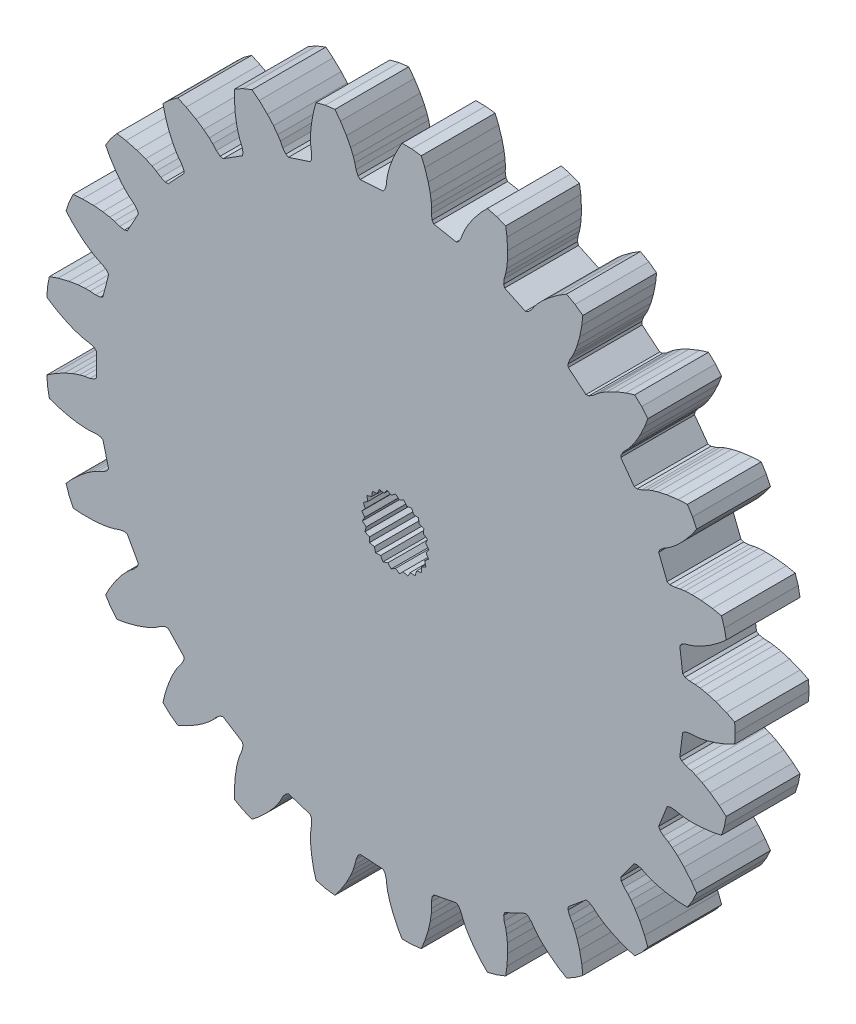
SolidWorks part; units mm, degrees
ref_plane "Front Plane" through (0, 0, 0) normal (0, 0, 1) x (1, 0, 0)
ref_plane "Top Plane" through (0, 0, 0) normal (0, 1, 0) x (1, 0, 0)
ref_plane "Right Plane" through (0, 0, 0) normal (1, 0, 0) x (0, 0, -1)
sketch "Model" plane through (0, 0, 0) normal (0, 0, 1) x (1, 0, 0)
  line L0 (28.0476, -8.5314) -> (28.3042, -7.7419)
  line L1 (28.3042, -7.7419) -> (28.4597, -6.9264)
  line L2 (28.4597, -6.9264) -> (27.8578, -6.4126)
  line L3 (27.8578, -6.4126) -> (27.0681, -5.8455)
  line L4 (27.0681, -5.8455) -> (26.3904, -5.4402)
  line L5 (26.3904, -5.4402) -> (25.8454, -5.1734)
  line L6 (25.8454, -5.1734) -> (25.4502, -5.0195)
  line L7 (25.4502, -5.0195) -> (24.9993, -4.8861)
  line L8 (24.9993, -4.8861) -> (24.6274, -4.699)
  line L9 (24.6274, -4.699) -> (24.4647, -4.4976)
  line L10 (24.4647, -4.4976) -> (24.7116, -2.5433)
  line L11 (24.7116, -2.5433) -> (24.9192, -2.3886)
  line L12 (24.9192, -2.3886) -> (25.326, -2.2999)
  line L13 (25.326, -2.2999) -> (25.7959, -2.2828)
  line L14 (25.7959, -2.2828) -> (26.217, -2.232)
  line L15 (26.217, -2.232) -> (26.8112, -2.1091)
  line L16 (26.8112, -2.1091) -> (27.5684, -1.8851)
  line L17 (27.5684, -1.8851) -> (28.4744, -1.5322)
  line L18 (28.4744, -1.5322) -> (29.1851, -1.1843)
  line L19 (29.1851, -1.1843) -> (29.2372, -0.3558)
  line L20 (29.2372, -0.3558) -> (29.1851, 0.4728)
  line L21 (29.1851, 0.4728) -> (28.4744, 0.8207)
  line L22 (28.4744, 0.8207) -> (27.5684, 1.1736)
  line L23 (27.5684, 1.1736) -> (26.8112, 1.3976)
  line L24 (26.8112, 1.3976) -> (26.217, 1.5205)
  line L25 (26.217, 1.5205) -> (25.7959, 1.5713)
  line L26 (25.7959, 1.5713) -> (25.326, 1.5884)
  line L27 (25.326, 1.5884) -> (24.9192, 1.6771)
  line L28 (24.9192, 1.6771) -> (24.7116, 1.8317)
  line L29 (24.7116, 1.8317) -> (24.4647, 3.7861)
  line L30 (24.4647, 3.7861) -> (24.6274, 3.9875)
  line L31 (24.6274, 3.9875) -> (24.9993, 4.1746)
  line L32 (24.9993, 4.1746) -> (25.4502, 4.308)
  line L33 (25.4502, 4.308) -> (25.8454, 4.4619)
  line L34 (25.8454, 4.4619) -> (26.3904, 4.7287)
  line L35 (26.3904, 4.7287) -> (27.0681, 5.134)
  line L36 (27.0681, 5.134) -> (27.8578, 5.7011)
  line L37 (27.8578, 5.7011) -> (28.4597, 6.2148)
  line L38 (28.4597, 6.2148) -> (28.3042, 7.0303)
  line L39 (28.3042, 7.0303) -> (28.0476, 7.8199)
  line L40 (28.0476, 7.8199) -> (27.2727, 7.9801)
  line L41 (27.2727, 7.9801) -> (26.3074, 8.0966)
  line L42 (26.3074, 8.0966) -> (25.5183, 8.1253)
  line L43 (25.5183, 8.1253) -> (24.9122, 8.0965)
  line L44 (24.9122, 8.0965) -> (24.4917, 8.041)
  line L45 (24.4917, 8.041) -> (24.0323, 7.9407)
  line L46 (24.0323, 7.9407) -> (23.6163, 7.9255)
  line L47 (23.6163, 7.9255) -> (23.3767, 8.0236)
  line L48 (23.3767, 8.0236) -> (22.6515, 9.8551)
  line L49 (22.6515, 9.8551) -> (22.759, 10.0907)
  line L50 (22.759, 10.0907) -> (23.0727, 10.3644)
  line L51 (23.0727, 10.3644) -> (23.4763, 10.6057)
  line L52 (23.4763, 10.6057) -> (23.8208, 10.8531)
  line L53 (23.8208, 10.8531) -> (24.2823, 11.2471)
  line L54 (24.2823, 11.2471) -> (24.8379, 11.8081)
  line L55 (24.8379, 11.8081) -> (25.4618, 12.5538)
  line L56 (25.4618, 12.5538) -> (25.917, 13.2011)
  line L57 (25.917, 13.2011) -> (25.5636, 13.9523)
  line L58 (25.5636, 13.9523) -> (25.1187, 14.6533)
  line L59 (25.1187, 14.6533) -> (24.3283, 14.6157)
  line L60 (24.3283, 14.6157) -> (23.3643, 14.4885)
  line L61 (23.3643, 14.4885) -> (22.5929, 14.3201)
  line L62 (22.5929, 14.3201) -> (22.013, 14.1415)
  line L63 (22.013, 14.1415) -> (21.6195, 13.9831)
  line L64 (21.6195, 13.9831) -> (21.1995, 13.7717)
  line L65 (21.1995, 13.7717) -> (20.8003, 13.6535)
  line L66 (20.8003, 13.6535) -> (20.5439, 13.689)
  line L67 (20.5439, 13.689) -> (19.386, 15.2826)
  line L68 (19.386, 15.2826) -> (19.4315, 15.5375)
  line L69 (19.4315, 15.5375) -> (19.6673, 15.8806)
  line L70 (19.6673, 15.8806) -> (19.9982, 16.2148)
  line L71 (19.9982, 16.2148) -> (20.2703, 16.54)
  line L72 (20.2703, 16.54) -> (20.6194, 17.0364)
  line L73 (20.6194, 17.0364) -> (21.018, 17.718)
  line L74 (21.018, 17.718) -> (21.4368, 18.5954)
  line L75 (21.4368, 18.5954) -> (21.7168, 19.3356)
  line L76 (21.7168, 19.3356) -> (21.1876, 19.9753)
  line L77 (21.1876, 19.9753) -> (20.5824, 20.5436)
  line L78 (20.5824, 20.5436) -> (19.8261, 20.3107)
  line L79 (19.8261, 20.3107) -> (18.9241, 19.9477)
  line L80 (18.9241, 19.9477) -> (18.2189, 19.5927)
  line L81 (18.2189, 19.5927) -> (17.7016, 19.2755)
  line L82 (17.7016, 19.2755) -> (17.3598, 19.0243)
  line L83 (17.3598, 19.0243) -> (17.0056, 18.7151)
  line L84 (17.0056, 18.7151) -> (16.6483, 18.5013)
  line L85 (16.6483, 18.5013) -> (16.3911, 18.4719)
  line L86 (16.3911, 18.4719) -> (14.8733, 19.7275)
  line L87 (14.8733, 19.7275) -> (14.854, 19.9857)
  line L88 (14.854, 19.9857) -> (14.997, 20.3767)
  line L89 (14.997, 20.3767) -> (15.2344, 20.7826)
  line L90 (15.2344, 20.7826) -> (15.4171, 21.1653)
  line L91 (15.4171, 21.1653) -> (15.6318, 21.7329)
  line L92 (15.6318, 21.7329) -> (15.8484, 22.4922)
  line L93 (15.8484, 22.4922) -> (16.0359, 23.4463)
  line L94 (16.0359, 23.4463) -> (16.1229, 24.2328)
  line L95 (16.1229, 24.2328) -> (15.4513, 24.7208)
  line L96 (15.4513, 24.7208) -> (14.7238, 25.1207)
  line L97 (14.7238, 25.1207) -> (14.0492, 24.707)
  line L98 (14.0492, 24.707) -> (13.2658, 24.1312)
  line L99 (13.2658, 24.1312) -> (12.671, 23.6119)
  line L100 (12.671, 23.6119) -> (12.2488, 23.176)
  line L101 (12.2488, 23.176) -> (11.9803, 22.8477)
  line L102 (11.9803, 22.8477) -> (11.7141, 22.4601)
  line L103 (11.7141, 22.4601) -> (11.4212, 22.1642)
  line L104 (11.4212, 22.1642) -> (11.1794, 22.0718)
  line L105 (11.1794, 22.0718) -> (9.397, 22.9105)
  line L106 (9.397, 22.9105) -> (9.3141, 23.1558)
  line L107 (9.3141, 23.1558) -> (9.3554, 23.57)
  line L108 (9.3554, 23.57) -> (9.4844, 24.0222)
  line L109 (9.4844, 24.0222) -> (9.5662, 24.4384)
  line L110 (9.5662, 24.4384) -> (9.6329, 25.0415)
  line L111 (9.6329, 25.0415) -> (9.6539, 25.8308)
  line L112 (9.6539, 25.8308) -> (9.5982, 26.8015)
  line L113 (9.5982, 26.8015) -> (9.4869, 27.585)
  line L114 (9.4869, 27.585) -> (8.7151, 27.8906)
  line L115 (8.7151, 27.8906) -> (7.9109, 28.0971)
  line L116 (7.9109, 28.0971) -> (7.3604, 27.5286)
  line L117 (7.3604, 27.5286) -> (6.7448, 26.776)
  line L118 (6.7448, 26.776) -> (6.2978, 26.1252)
  line L119 (6.2978, 26.1252) -> (5.9973, 25.598)
  line L120 (5.9973, 25.598) -> (5.8189, 25.2132)
  line L121 (5.8189, 25.2132) -> (5.6574, 24.7716)
  line L122 (5.6574, 24.7716) -> (5.4473, 24.4121)
  line L123 (5.4473, 24.4121) -> (5.2361, 24.2624)
  line L124 (5.2361, 24.2624) -> (3.3011, 24.6315)
  line L125 (3.3011, 24.6315) -> (3.1599, 24.8485)
  line L126 (3.1599, 24.8485) -> (3.0968, 25.26)
  line L127 (3.0968, 25.26) -> (3.1093, 25.7301)
  line L128 (3.1093, 25.7301) -> (3.085, 26.1535)
  line L129 (3.085, 26.1535) -> (2.9997, 26.7543)
  line L130 (2.9997, 26.7543) -> (2.8237, 27.524)
  line L131 (2.8237, 27.524) -> (2.5284, 28.4504)
  line L132 (2.5284, 28.4504) -> (2.2258, 29.1816)
  line L133 (2.2258, 29.1816) -> (1.4021, 29.2856)
  line L134 (1.4021, 29.2856) -> (0.5719, 29.2856)
  line L135 (0.5719, 29.2856) -> (0.1801, 28.5981)
  line L136 (0.1801, 28.5981) -> (-0.229, 27.7161)
  line L137 (-0.229, 27.7161) -> (-0.5001, 26.9745)
  line L138 (-0.5001, 26.9745) -> (-0.6601, 26.3891)
  line L139 (-0.6601, 26.3891) -> (-0.7372, 25.9721)
  line L140 (-0.7372, 25.9721) -> (-0.7838, 25.5042)
  line L141 (-0.7838, 25.5042) -> (-0.8979, 25.1038)
  line L142 (-0.8979, 25.1038) -> (-1.0652, 24.9063)
  line L143 (-1.0652, 24.9063) -> (-3.0312, 24.7826)
  line L144 (-3.0312, 24.7826) -> (-3.222, 24.9576)
  line L145 (-3.222, 24.9576) -> (-3.3854, 25.3405)
  line L146 (-3.3854, 25.3405) -> (-3.4902, 25.7989)
  line L147 (-3.4902, 25.7989) -> (-3.619, 26.203)
  line L148 (-3.619, 26.203) -> (-3.8511, 26.7637)
  line L149 (-3.8511, 26.7637) -> (-4.213, 27.4654)
  line L150 (-4.213, 27.4654) -> (-4.7294, 28.2892)
  line L151 (-4.7294, 28.2892) -> (-5.2043, 28.9222)
  line L152 (-5.2043, 28.9222) -> (-6.028, 28.8182)
  line L153 (-6.028, 28.8182) -> (-6.8321, 28.6117)
  line L154 (-6.8321, 28.6117) -> (-7.0407, 27.8483)
  line L155 (-7.0407, 27.8483) -> (-7.2175, 26.8923)
  line L156 (-7.2175, 26.8923) -> (-7.2957, 26.1066)
  line L157 (-7.2957, 26.1066) -> (-7.305, 25.4998)
  line L158 (-7.305, 25.4998) -> (-7.2761, 25.0767)
  line L159 (-7.2761, 25.0767) -> (-7.2048, 24.6119)
  line L160 (-7.2048, 24.6119) -> (-7.2157, 24.1957)
  line L161 (-7.2157, 24.1957) -> (-7.3287, 23.9628)
  line L162 (-7.3287, 23.9628) -> (-9.2022, 23.354)
  line L163 (-9.2022, 23.354) -> (-9.4305, 23.4761)
  line L164 (-9.4305, 23.4761) -> (-9.684, 23.8064)
  line L165 (-9.684, 23.8064) -> (-9.8995, 24.2243)
  line L166 (-9.8995, 24.2243) -> (-10.1248, 24.5836)
  line L167 (-10.1248, 24.5836) -> (-10.489, 25.069)
  line L168 (-10.489, 25.069) -> (-11.014, 25.6587)
  line L169 (-11.014, 25.6587) -> (-11.7191, 26.3282)
  line L170 (-11.7191, 26.3282) -> (-12.3365, 26.8232)
  line L171 (-12.3365, 26.8232) -> (-13.1084, 26.5176)
  line L172 (-13.1084, 26.5176) -> (-13.8359, 26.1176)
  line L173 (-13.8359, 26.1176) -> (-13.8481, 25.3264)
  line L174 (-13.8481, 25.3264) -> (-13.7816, 24.3564)
  line L175 (-13.7816, 24.3564) -> (-13.662, 23.5759)
  line L176 (-13.662, 23.5759) -> (-13.5201, 22.9859)
  line L177 (-13.5201, 22.9859) -> (-13.3868, 22.5833)
  line L178 (-13.3868, 22.5833) -> (-13.2022, 22.1508)
  line L179 (-13.2022, 22.1508) -> (-13.1093, 21.745)
  line L180 (-13.1093, 21.745) -> (-13.1608, 21.4913)
  line L181 (-13.1608, 21.4913) -> (-14.824, 20.4358)
  line L182 (-14.824, 20.4358) -> (-15.0755, 20.4972)
  line L183 (-15.0755, 20.4972) -> (-15.4031, 20.7541)
  line L184 (-15.4031, 20.7541) -> (-15.7158, 21.1052)
  line L185 (-15.7158, 21.1052) -> (-16.0234, 21.3973)
  line L186 (-16.0234, 21.3973) -> (-16.4969, 21.7769)
  line L187 (-16.4969, 21.7769) -> (-17.1521, 22.2174)
  line L188 (-17.1521, 22.2174) -> (-18.0015, 22.6906)
  line L189 (-18.0015, 22.6906) -> (-18.7226, 23.0165)
  line L190 (-18.7226, 23.0165) -> (-19.3942, 22.5285)
  line L191 (-19.3942, 22.5285) -> (-19.9994, 21.9602)
  line L192 (-19.9994, 21.9602) -> (-19.8144, 21.1907)
  line L193 (-19.8144, 21.1907) -> (-19.5089, 20.2677)
  line L194 (-19.5089, 20.2677) -> (-19.1989, 19.5416)
  line L195 (-19.1989, 19.5416) -> (-18.9147, 19.0054)
  line L196 (-18.9147, 19.0054) -> (-18.6855, 18.6485)
  line L197 (-18.6855, 18.6485) -> (-18.3991, 18.2756)
  line L198 (-18.3991, 18.2756) -> (-18.2082, 17.9056)
  line L199 (-18.2082, 17.9056) -> (-18.195, 17.647)
  line L200 (-18.195, 17.647) -> (-19.5434, 16.2111)
  line L201 (-19.5434, 16.2111) -> (-19.8023, 16.208)
  line L202 (-19.8023, 16.208) -> (-20.1836, 16.3753)
  line L203 (-20.1836, 16.3753) -> (-20.5738, 16.6377)
  line L204 (-20.5738, 16.6377) -> (-20.9443, 16.8441)
  line L205 (-20.9443, 16.8441) -> (-21.4973, 17.094)
  line L206 (-21.4973, 17.094) -> (-22.2415, 17.3578)
  line L207 (-22.2415, 17.3578) -> (-23.1819, 17.6048)
  line L208 (-23.1819, 17.6048) -> (-23.9614, 17.7411)
  line L209 (-23.9614, 17.7411) -> (-24.4906, 17.1015)
  line L210 (-24.4906, 17.1015) -> (-24.9354, 16.4005)
  line L211 (-24.9354, 16.4005) -> (-24.5649, 15.7013)
  line L212 (-24.5649, 15.7013) -> (-24.0393, 14.8832)
  line L213 (-24.0393, 14.8832) -> (-23.5585, 14.257)
  line L214 (-23.5585, 14.257) -> (-23.1499, 13.8083)
  line L215 (-23.1499, 13.8083) -> (-22.8392, 13.5197)
  line L216 (-22.8392, 13.5197) -> (-22.469, 13.2296)
  line L217 (-22.469, 13.2296) -> (-22.1921, 12.9188)
  line L218 (-22.1921, 12.9188) -> (-22.115, 12.6716)
  line L219 (-22.115, 12.6716) -> (-23.064, 10.9454)
  line L220 (-23.064, 10.9454) -> (-23.314, 10.8781)
  line L221 (-23.314, 10.8781) -> (-23.7248, 10.9453)
  line L222 (-23.7248, 10.9453) -> (-24.1681, 11.1024)
  line L223 (-24.1681, 11.1024) -> (-24.5782, 11.2102)
  line L224 (-24.5782, 11.2102) -> (-25.176, 11.3147)
  line L225 (-25.176, 11.3147) -> (-25.9624, 11.3851)
  line L226 (-25.9624, 11.3851) -> (-26.9347, 11.3905)
  line L227 (-26.9347, 11.3905) -> (-27.7236, 11.3287)
  line L228 (-27.7236, 11.3287) -> (-28.0771, 10.5775)
  line L229 (-28.0771, 10.5775) -> (-28.3337, 9.788)
  line L230 (-28.3337, 9.788) -> (-27.8009, 9.2028)
  line L231 (-27.8009, 9.2028) -> (-27.0884, 8.5412)
  line L232 (-27.0884, 8.5412) -> (-26.4669, 8.0542)
  line L233 (-26.4669, 8.0542) -> (-25.9596, 7.7212)
  line L234 (-25.9596, 7.7212) -> (-25.5868, 7.519)
  line L235 (-25.5868, 7.519) -> (-25.1562, 7.3301)
  line L236 (-25.1562, 7.3301) -> (-24.8107, 7.0979)
  line L237 (-24.8107, 7.0979) -> (-24.6745, 6.8776)
  line L238 (-24.6745, 6.8776) -> (-25.1644, 4.9697)
  line L239 (-25.1644, 4.9697) -> (-25.3898, 4.8423)
  line L240 (-25.3898, 4.8423) -> (-25.8045, 4.8052)
  line L241 (-25.8045, 4.8052) -> (-26.2728, 4.8472)
  line L242 (-26.2728, 4.8472) -> (-26.6969, 4.8495)
  line L243 (-26.6969, 4.8495) -> (-27.3019, 4.8021)
  line L244 (-27.3019, 4.8021) -> (-28.0812, 4.6748)
  line L245 (-28.0812, 4.6748) -> (-29.0242, 4.4382)
  line L246 (-29.0242, 4.4382) -> (-29.773, 4.1821)
  line L247 (-29.773, 4.1821) -> (-29.9286, 3.3666)
  line L248 (-29.9286, 3.3666) -> (-29.9807, 2.5381)
  line L249 (-29.9807, 2.5381) -> (-29.3191, 2.1038)
  line L250 (-29.3191, 2.1038) -> (-28.4645, 1.6402)
  line L251 (-28.4645, 1.6402) -> (-27.7414, 1.323)
  line L252 (-27.7414, 1.323) -> (-27.1673, 1.1266)
  line L253 (-27.1673, 1.1266) -> (-26.7559, 1.0235)
  line L254 (-26.7559, 1.0235) -> (-26.2918, 0.9476)
  line L255 (-26.2918, 0.9476) -> (-25.8994, 0.8086)
  line L256 (-25.8994, 0.8086) -> (-25.7128, 0.6292)
  line L257 (-25.7128, 0.6292) -> (-25.7128, -1.3407)
  line L258 (-25.7128, -1.3407) -> (-25.8994, -1.5201)
  line L259 (-25.8994, -1.5201) -> (-26.2918, -1.6591)
  line L260 (-26.2918, -1.6591) -> (-26.7559, -1.735)
  line L261 (-26.7559, -1.735) -> (-27.1673, -1.8382)
  line L262 (-27.1673, -1.8382) -> (-27.7414, -2.0346)
  line L263 (-27.7414, -2.0346) -> (-28.4645, -2.3517)
  line L264 (-28.4645, -2.3517) -> (-29.3191, -2.8154)
  line L265 (-29.3191, -2.8154) -> (-29.9807, -3.2496)
  line L266 (-29.9807, -3.2496) -> (-29.9286, -4.0782)
  line L267 (-29.9286, -4.0782) -> (-29.773, -4.8937)
  line L268 (-29.773, -4.8937) -> (-29.0242, -5.1497)
  line L269 (-29.0242, -5.1497) -> (-28.0812, -5.3863)
  line L270 (-28.0812, -5.3863) -> (-27.3019, -5.5137)
  line L271 (-27.3019, -5.5137) -> (-26.6969, -5.5611)
  line L272 (-26.6969, -5.5611) -> (-26.2728, -5.5587)
  line L273 (-26.2728, -5.5587) -> (-25.8045, -5.5168)
  line L274 (-25.8045, -5.5168) -> (-25.3898, -5.5538)
  line L275 (-25.3898, -5.5538) -> (-25.1644, -5.6812)
  line L276 (-25.1644, -5.6812) -> (-24.6745, -7.5892)
  line L277 (-24.6745, -7.5892) -> (-24.8107, -7.8094)
  line L278 (-24.8107, -7.8094) -> (-25.1562, -8.0416)
  line L279 (-25.1562, -8.0416) -> (-25.5868, -8.2305)
  line L280 (-25.5868, -8.2305) -> (-25.9596, -8.4327)
  line L281 (-25.9596, -8.4327) -> (-26.4669, -8.7657)
  line L282 (-26.4669, -8.7657) -> (-27.0884, -9.2527)
  line L283 (-27.0884, -9.2527) -> (-27.8009, -9.9144)
  line L284 (-27.8009, -9.9144) -> (-28.3337, -10.4995)
  line L285 (0.0008, 2.8698) -> (-0.3313, 2.6039)
  line L286 (0.0008, 2.8698) -> (0.3329, 2.6039)
  line L287 (0.7207, 2.7788) -> (0.3329, 2.6039)
  line L288 (0.7207, 2.7788) -> (0.9763, 2.4387)
  line L289 (1.3955, 2.5117) -> (0.9763, 2.4387)
  line L290 (1.3955, 2.5117) -> (1.5584, 2.1187)
  line L291 (1.9826, 2.0851) -> (1.5584, 2.1187)
  line L292 (1.9826, 2.0851) -> (2.0426, 1.6639)
  line L293 (2.4451, 1.526) -> (2.0426, 1.6639)
  line L294 (2.4451, 1.526) -> (2.3986, 1.1031)
  line L295 (2.7541, 0.8694) -> (2.3986, 1.1031)
  line L296 (2.7541, 0.8694) -> (2.6038, 0.4713)
  line L297 (2.8901, 0.1565) -> (2.6038, 0.4713)
  line L298 (2.8901, 0.1565) -> (2.6456, -0.1916)
  line L299 (2.8445, -0.5677) -> (2.6456, -0.1916)
  line L300 (2.8445, -0.5677) -> (2.5211, -0.8441)
  line L301 (2.6203, -1.2579) -> (2.5211, -0.8441)
  line L302 (2.6203, -1.2579) -> (2.2383, -1.4452)
  line L303 (2.2314, -1.8706) -> (2.2383, -1.4452)
  line L304 (2.2314, -1.8706) -> (1.8148, -1.957)
  line L305 (1.7024, -2.3673) -> (1.8148, -1.957)
  line L306 (1.7024, -2.3673) -> (1.2774, -2.3474)
  line L307 (1.0665, -2.7169) -> (1.2774, -2.3474)
  line L308 (1.0665, -2.7169) -> (0.6598, -2.592)
  line L309 (0.3636, -2.8974) -> (0.6598, -2.592)
  line L310 (0.3636, -2.8974) -> (0.0008, -2.6752)
  line L311 (-0.3621, -2.8974) -> (0.0008, -2.6752)
  line L312 (-0.3621, -2.8974) -> (-0.6582, -2.592)
  line L313 (-1.0649, -2.7169) -> (-0.6582, -2.592)
  line L314 (-1.0649, -2.7169) -> (-1.2759, -2.3474)
  line L315 (-1.7009, -2.3673) -> (-1.2759, -2.3474)
  line L316 (-1.7009, -2.3673) -> (-1.8133, -1.957)
  line L317 (-2.2298, -1.8706) -> (-1.8133, -1.957)
  line L318 (-2.2298, -1.8706) -> (-2.2367, -1.4452)
  line L319 (-2.6187, -1.2579) -> (-2.2367, -1.4452)
  line L320 (-2.6187, -1.2579) -> (-2.5195, -0.8441)
  line L321 (-2.8429, -0.5677) -> (-2.5195, -0.8441)
  line L322 (-2.8429, -0.5677) -> (-2.644, -0.1916)
  line L323 (-2.8885, 0.1565) -> (-2.644, -0.1916)
  line L324 (-2.8885, 0.1565) -> (-2.6023, 0.4713)
  line L325 (-2.7525, 0.8694) -> (-2.6023, 0.4713)
  line L326 (-2.7525, 0.8694) -> (-2.397, 1.1031)
  line L327 (-2.4435, 1.526) -> (-2.397, 1.1031)
  line L328 (-2.4435, 1.526) -> (-2.0411, 1.6639)
  line L329 (-1.981, 2.0851) -> (-2.0411, 1.6639)
  line L330 (-1.981, 2.0851) -> (-1.5568, 2.1187)
  line L331 (-1.3939, 2.5117) -> (-1.5568, 2.1187)
  line L332 (-1.3939, 2.5117) -> (-0.9747, 2.4387)
  line L333 (-0.7192, 2.7788) -> (-0.9747, 2.4387)
  line L334 (-0.7192, 2.7788) -> (-0.3313, 2.6039)
  line L620 (-28.3337, -10.4995) -> (-28.0771, -11.2891)
  line L621 (-28.0771, -11.2891) -> (-27.7236, -12.0402)
  line L622 (-27.7236, -12.0402) -> (-26.9347, -12.1021)
  line L623 (-26.9347, -12.1021) -> (-25.9624, -12.0967)
  line L624 (-25.9624, -12.0967) -> (-25.176, -12.0262)
  line L625 (-25.176, -12.0262) -> (-24.5782, -11.9217)
  line L626 (-24.5782, -11.9217) -> (-24.1681, -11.814)
  line L627 (-24.1681, -11.814) -> (-23.7248, -11.6569)
  line L628 (-23.7248, -11.6569) -> (-23.314, -11.5896)
  line L629 (-23.314, -11.5896) -> (-23.064, -11.6569)
  line L630 (-23.064, -11.6569) -> (-22.115, -13.3832)
  line L631 (-22.115, -13.3832) -> (-22.1921, -13.6303)
  line L632 (-22.1921, -13.6303) -> (-22.469, -13.9412)
  line L633 (-22.469, -13.9412) -> (-22.8392, -14.2312)
  line L634 (-22.8392, -14.2312) -> (-23.1499, -14.5198)
  line L635 (-23.1499, -14.5198) -> (-23.5585, -14.9685)
  line L636 (-23.5585, -14.9685) -> (-24.0393, -15.5948)
  line L637 (-24.0393, -15.5948) -> (-24.5649, -16.4128)
  line L638 (-24.5649, -16.4128) -> (-24.9354, -17.112)
  line L639 (-24.9354, -17.112) -> (-24.4906, -17.813)
  line L640 (-24.4906, -17.813) -> (-23.9614, -18.4527)
  line L641 (-23.9614, -18.4527) -> (-23.1819, -18.3164)
  line L642 (-23.1819, -18.3164) -> (-22.2415, -18.0693)
  line L643 (-22.2415, -18.0693) -> (-21.4973, -17.8055)
  line L644 (-21.4973, -17.8055) -> (-20.9443, -17.5556)
  line L645 (-20.9443, -17.5556) -> (-20.5738, -17.3493)
  line L646 (-20.5738, -17.3493) -> (-20.1836, -17.0869)
  line L647 (-20.1836, -17.0869) -> (-19.8023, -16.9196)
  line L648 (-19.8023, -16.9196) -> (-19.5434, -16.9226)
  line L649 (-19.5434, -16.9226) -> (-18.195, -18.3586)
  line L650 (-18.195, -18.3586) -> (-18.2082, -18.6171)
  line L651 (-18.2082, -18.6171) -> (-18.3991, -18.9871)
  line L652 (-18.3991, -18.9871) -> (-18.6855, -19.3601)
  line L653 (-18.6855, -19.3601) -> (-18.9147, -19.7169)
  line L654 (-18.9147, -19.7169) -> (-19.1989, -20.2531)
  line L655 (-19.1989, -20.2531) -> (-19.5089, -20.9793)
  line L656 (-19.5089, -20.9793) -> (-19.8144, -21.9023)
  line L657 (-19.8144, -21.9023) -> (-19.9994, -22.6717)
  line L658 (-19.9994, -22.6717) -> (-19.3942, -23.24)
  line L659 (-19.3942, -23.24) -> (-18.7226, -23.728)
  line L660 (-18.7226, -23.728) -> (-18.0015, -23.4021)
  line L661 (-18.0015, -23.4021) -> (-17.1521, -22.929)
  line L662 (-17.1521, -22.929) -> (-16.4969, -22.4884)
  line L663 (-16.4969, -22.4884) -> (-16.0234, -22.1088)
  line L664 (-16.0234, -22.1088) -> (-15.7158, -21.8168)
  line L665 (-15.7158, -21.8168) -> (-15.4031, -21.4656)
  line L666 (-15.4031, -21.4656) -> (-15.0755, -21.2087)
  line L667 (-15.0755, -21.2087) -> (-14.824, -21.1473)
  line L668 (-14.824, -21.1473) -> (-13.1608, -22.2028)
  line L669 (-13.1608, -22.2028) -> (-13.1093, -22.4565)
  line L670 (-13.1093, -22.4565) -> (-13.2022, -22.8624)
  line L671 (-13.2022, -22.8624) -> (-13.3868, -23.2948)
  line L672 (-13.3868, -23.2948) -> (-13.5201, -23.6974)
  line L673 (-13.5201, -23.6974) -> (-13.662, -24.2875)
  line L674 (-13.662, -24.2875) -> (-13.7816, -25.0679)
  line L675 (-13.7816, -25.0679) -> (-13.8481, -26.0379)
  line L676 (-13.8481, -26.0379) -> (-13.8359, -26.8292)
  line L677 (-13.8359, -26.8292) -> (-13.1084, -27.2291)
  line L678 (-13.1084, -27.2291) -> (-12.3365, -27.5347)
  line L679 (-12.3365, -27.5347) -> (-11.7191, -27.0398)
  line L680 (-11.7191, -27.0398) -> (-11.014, -26.3703)
  line L681 (-11.014, -26.3703) -> (-10.489, -25.7806)
  line L682 (-10.489, -25.7806) -> (-10.1248, -25.2952)
  line L683 (-10.1248, -25.2952) -> (-9.8995, -24.9358)
  line L684 (-9.8995, -24.9358) -> (-9.684, -24.5179)
  line L685 (-9.684, -24.5179) -> (-9.4305, -24.1876)
  line L686 (-9.4305, -24.1876) -> (-9.2022, -24.0656)
  line L687 (-9.2022, -24.0656) -> (-7.3287, -24.6743)
  line L688 (-7.3287, -24.6743) -> (-7.2157, -24.9073)
  line L689 (-7.2157, -24.9073) -> (-7.2048, -25.3234)
  line L690 (-7.2048, -25.3234) -> (-7.2761, -25.7882)
  line L691 (-7.2761, -25.7882) -> (-7.305, -26.2114)
  line L692 (-7.305, -26.2114) -> (-7.2957, -26.8181)
  line L693 (-7.2957, -26.8181) -> (-7.2175, -27.6038)
  line L694 (-7.2175, -27.6038) -> (-7.0407, -28.5599)
  line L695 (-7.0407, -28.5599) -> (-6.8321, -29.3232)
  line L696 (-6.8321, -29.3232) -> (-6.028, -29.5297)
  line L697 (-6.028, -29.5297) -> (-5.2043, -29.6337)
  line L698 (-5.2043, -29.6337) -> (-4.7294, -29.0008)
  line L699 (-4.7294, -29.0008) -> (-4.213, -28.177)
  line L700 (-4.213, -28.177) -> (-3.8511, -27.4752)
  line L701 (-3.8511, -27.4752) -> (-3.619, -26.9145)
  line L702 (-3.619, -26.9145) -> (-3.4902, -26.5104)
  line L703 (-3.4902, -26.5104) -> (-3.3854, -26.052)
  line L704 (-3.3854, -26.052) -> (-3.222, -25.6691)
  line L705 (-3.222, -25.6691) -> (-3.0312, -25.4941)
  line L706 (-3.0312, -25.4941) -> (-1.0652, -25.6178)
  line L707 (-1.0652, -25.6178) -> (-0.8979, -25.8153)
  line L708 (-0.8979, -25.8153) -> (-0.7838, -26.2157)
  line L709 (-0.7838, -26.2157) -> (-0.7372, -26.6836)
  line L710 (-0.7372, -26.6836) -> (-0.6601, -27.1007)
  line L711 (-0.6601, -27.1007) -> (-0.5001, -27.686)
  line L712 (-0.5001, -27.686) -> (-0.229, -28.4276)
  line L713 (-0.229, -28.4276) -> (0.1801, -29.3096)
  line L714 (0.1801, -29.3096) -> (0.5719, -29.9972)
  line L715 (0.5719, -29.9972) -> (1.4021, -29.9972)
  line L716 (1.4021, -29.9972) -> (2.2258, -29.8931)
  line L717 (2.2258, -29.8931) -> (2.5284, -29.1619)
  line L718 (2.5284, -29.1619) -> (2.8237, -28.2355)
  line L719 (2.8237, -28.2355) -> (2.9997, -27.4658)
  line L720 (2.9997, -27.4658) -> (3.085, -26.865)
  line L721 (3.085, -26.865) -> (3.1093, -26.4416)
  line L722 (3.1093, -26.4416) -> (3.0968, -25.9716)
  line L723 (3.0968, -25.9716) -> (3.1599, -25.56)
  line L724 (3.1599, -25.56) -> (3.3011, -25.3431)
  line L725 (3.3011, -25.3431) -> (5.2361, -24.974)
  line L726 (5.2361, -24.974) -> (5.4473, -25.1237)
  line L727 (5.4473, -25.1237) -> (5.6574, -25.4831)
  line L728 (5.6574, -25.4831) -> (5.8189, -25.9247)
  line L729 (5.8189, -25.9247) -> (5.9973, -26.3095)
  line L730 (5.9973, -26.3095) -> (6.2978, -26.8367)
  line L731 (6.2978, -26.8367) -> (6.7448, -27.4875)
  line L732 (6.7448, -27.4875) -> (7.3604, -28.2401)
  line L733 (7.3604, -28.2401) -> (7.9109, -28.8086)
  line L734 (7.9109, -28.8086) -> (8.7151, -28.6021)
  line L735 (8.7151, -28.6021) -> (9.4869, -28.2965)
  line L736 (9.4869, -28.2965) -> (9.5982, -27.513)
  line L737 (9.5982, -27.513) -> (9.6539, -26.5423)
  line L738 (9.6539, -26.5423) -> (9.6329, -25.7531)
  line L739 (9.6329, -25.7531) -> (9.5662, -25.1499)
  line L740 (9.5662, -25.1499) -> (9.4844, -24.7338)
  line L741 (9.4844, -24.7338) -> (9.3554, -24.2816)
  line L742 (9.3554, -24.2816) -> (9.3141, -23.8673)
  line L743 (9.3141, -23.8673) -> (9.397, -23.622)
  line L744 (9.397, -23.622) -> (11.1794, -22.7833)
  line L745 (11.1794, -22.7833) -> (11.4212, -22.8758)
  line L746 (11.4212, -22.8758) -> (11.7141, -23.1717)
  line L747 (11.7141, -23.1717) -> (11.9803, -23.5593)
  line L748 (11.9803, -23.5593) -> (12.2488, -23.8875)
  line L749 (12.2488, -23.8875) -> (12.671, -24.3235)
  line L750 (12.671, -24.3235) -> (13.2658, -24.8427)
  line L751 (13.2658, -24.8427) -> (14.0492, -25.4186)
  line L752 (14.0492, -25.4186) -> (14.7238, -25.8323)
  line L753 (14.7238, -25.8323) -> (15.4513, -25.4323)
  line L754 (15.4513, -25.4323) -> (16.1229, -24.9443)
  line L755 (16.1229, -24.9443) -> (16.0359, -24.1578)
  line L756 (16.0359, -24.1578) -> (15.8484, -23.2037)
  line L757 (15.8484, -23.2037) -> (15.6318, -22.4445)
  line L758 (15.6318, -22.4445) -> (15.4171, -21.8769)
  line L759 (15.4171, -21.8769) -> (15.2344, -21.4941)
  line L760 (15.2344, -21.4941) -> (14.997, -21.0882)
  line L761 (14.997, -21.0882) -> (14.854, -20.6972)
  line L762 (14.854, -20.6972) -> (14.8733, -20.439)
  line L763 (14.8733, -20.439) -> (16.3911, -19.1834)
  line L764 (16.3911, -19.1834) -> (16.6483, -19.2128)
  line L765 (16.6483, -19.2128) -> (17.0056, -19.4266)
  line L766 (17.0056, -19.4266) -> (17.3598, -19.7358)
  line L767 (17.3598, -19.7358) -> (17.7016, -19.987)
  line L768 (17.7016, -19.987) -> (18.2189, -20.3043)
  line L769 (18.2189, -20.3043) -> (18.9241, -20.6593)
  line L770 (18.9241, -20.6593) -> (19.8261, -21.0222)
  line L771 (19.8261, -21.0222) -> (20.5824, -21.2551)
  line L772 (20.5824, -21.2551) -> (21.1876, -20.6868)
  line L773 (21.1876, -20.6868) -> (21.7168, -20.0471)
  line L774 (21.7168, -20.0471) -> (21.4368, -19.307)
  line L775 (21.4368, -19.307) -> (21.018, -18.4295)
  line L776 (21.018, -18.4295) -> (20.6194, -17.7479)
  line L777 (20.6194, -17.7479) -> (20.2703, -17.2516)
  line L778 (20.2703, -17.2516) -> (19.9982, -16.9263)
  line L779 (19.9982, -16.9263) -> (19.6673, -16.5922)
  line L780 (19.6673, -16.5922) -> (19.4315, -16.249)
  line L781 (19.4315, -16.249) -> (19.386, -15.9942)
  line L782 (19.386, -15.9942) -> (20.5439, -14.4005)
  line L783 (20.5439, -14.4005) -> (20.8003, -14.3651)
  line L784 (20.8003, -14.3651) -> (21.1995, -14.4833)
  line L785 (21.1995, -14.4833) -> (21.6195, -14.6947)
  line L786 (21.6195, -14.6947) -> (22.013, -14.853)
  line L787 (22.013, -14.853) -> (22.5929, -15.0316)
  line L788 (22.5929, -15.0316) -> (23.3643, -15.2001)
  line L789 (23.3643, -15.2001) -> (24.3283, -15.3273)
  line L790 (24.3283, -15.3273) -> (25.1187, -15.3648)
  line L791 (25.1187, -15.3648) -> (25.5636, -14.6639)
  line L792 (25.5636, -14.6639) -> (25.917, -13.9127)
  line L793 (25.917, -13.9127) -> (25.4618, -13.2654)
  line L794 (25.4618, -13.2654) -> (24.8379, -12.5197)
  line L795 (24.8379, -12.5197) -> (24.2823, -11.9586)
  line L796 (24.2823, -11.9586) -> (23.8208, -11.5647)
  line L797 (23.8208, -11.5647) -> (23.4763, -11.3173)
  line L798 (23.4763, -11.3173) -> (23.0727, -11.0759)
  line L799 (23.0727, -11.0759) -> (22.759, -10.8022)
  line L800 (22.759, -10.8022) -> (22.6515, -10.5667)
  line L801 (22.6515, -10.5667) -> (23.3767, -8.7351)
  line L802 (23.3767, -8.7351) -> (23.6163, -8.637)
  line L803 (23.6163, -8.637) -> (24.0323, -8.6522)
  line L804 (24.0323, -8.6522) -> (24.4917, -8.7526)
  line L805 (24.4917, -8.7526) -> (24.9122, -8.808)
  line L806 (24.9122, -8.808) -> (25.5183, -8.8368)
  line L807 (25.5183, -8.8368) -> (26.3074, -8.8081)
  line L808 (26.3074, -8.8081) -> (27.2727, -8.6916)
  line L809 (27.2727, -8.6916) -> (28.0476, -8.5314)
  point P335 (0, 0)
  point P336 (0, 0)
extrude "Boss-Extrude1" add sketch "Model" along normal blind 6.35
